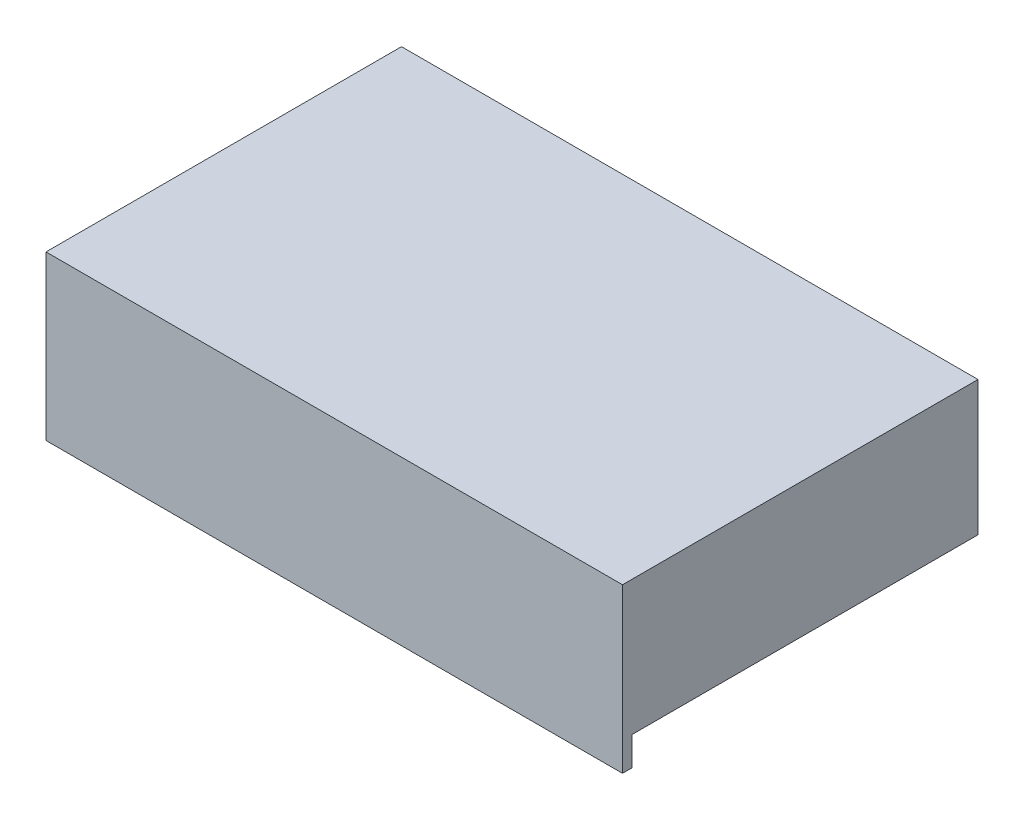
SolidWorks part; units mm, degrees
ref_plane "Front Plane" through (0, 0, 0) normal (0, 0, 1) x (1, 0, 0)
ref_plane "Top Plane" through (0, 0, 0) normal (0, 1, 0) x (1, 0, 0)
ref_plane "Right Plane" through (0, 0, 0) normal (1, 0, 0) x (0, 0, -1)
sketch "Sketch1" plane through (0, 0, 0) normal (0, 1, 0) x (1, 0, 0)
  line L1 (381, -228.6) -> (-381, -228.6)
  line L2 (381, -228.6) -> (381, 228.6)
  line L3 (381, 228.6) -> (-381, 228.6)
  line L4 (-381, -228.6) -> (-381, 228.6)
  line L5 (381, -228.6) -> (-381, 228.6) construction
  line L6 (381, 228.6) -> (-381, -228.6) construction
  point P0 (0, 0)
  dimension "D1" = 762
  dimension "D2" = 457.2
extrude "Boss-Extrude1" add sketch "Sketch1" along normal blind 177.8
sketch "Sketch2" plane through (0, 0, 0) normal (0, -1, 0) x (1, 0, 0)
  line L0 (-381, -228.6) -> (-381, 228.6) construction
  line L1 (374.65, -222.25) -> (-374.65, -222.25)
  line L2 (374.65, -222.25) -> (374.65, 222.25)
  line L3 (374.65, 222.25) -> (-374.65, 222.25)
  line L4 (-374.65, -222.25) -> (-374.65, 222.25)
  line L5 (374.65, -222.25) -> (-374.65, 222.25) construction
  line L6 (374.65, 222.25) -> (-374.65, -222.25) construction
  line L7 (-381, 228.6) -> (381, 228.6) construction
  point P0 (0, 0)
  dimension "D1" = 6.35
  dimension "D2" = 6.35
extrude "Cut-Extrude1" cut sketch "Sketch2" against normal blind 171.45
sketch "Sketch4" plane through (0, 0, 0) normal (0, -1, 0) x (1, 0, 0)
  line L0 (-381, 228.6) -> (381, 228.6) construction
  line L1 (379.4125, -227.0125) -> (-379.4125, -227.0125)
  line L2 (379.4125, -227.0125) -> (379.4125, 227.0125)
  line L3 (379.4125, 227.0125) -> (-379.4125, 227.0125)
  line L4 (-379.4125, -227.0125) -> (-379.4125, 227.0125)
  line L7 (-381, -228.6) -> (-381, 228.6) construction
  line L8 (-374.65, 222.25) -> (-374.65, -222.25) construction
  line L9 (376.2375, -223.8375) -> (-376.2375, -223.8375)
  line L10 (376.2375, -223.8375) -> (376.2375, 223.8375)
  line L11 (376.2375, 223.8375) -> (-376.2375, 223.8375)
  line L12 (-376.2375, -223.8375) -> (-376.2375, 223.8375)
  line L15 (374.65, 222.25) -> (-374.65, 222.25) construction
  point P0 (0, 0)
  point P10 (0, 0)
  dimension "D1" = 1.5875
  dimension "D2" = 1.5875
  dimension "D3" = 1.5875
  dimension "D4" = 1.5875
extrude "Cut-Extrude3" cut sketch "Sketch4" against normal blind 3.175
sketch "Sketch5" plane through (0, 0, 0) normal (0, 1, 0) x (1, 0, 0)
  line L0 (-1000, 0) -> (49000, 0) construction
  line L1 (0, -1000) -> (0, 49000) construction
  line L2 (-381, -228.6) -> (381, -228.6) construction
  line L4 (-381, -228.6) -> (381, -228.6)
  line L5 (-381, -228.6) -> (-381, -241.3)
  line L6 (-381, -241.3) -> (381, -241.3)
  line L7 (381, -228.6) -> (381, -241.3)
  dimension "D1" = 12.7
extrude "Boss-Extrude2" add sketch "Sketch5" along normal blind 177.8 and the other way blind 38.1
sketch "Sketch7" plane through (-381, 0, 0) normal (-1, 0, 0) x (0, 0, 1)
  line L0 (-228.6, 0) -> (228.6, 0) construction
  line L1 (-228.6, 177.8) -> (-228.6, 0) construction
  line L2 (-238.125, 9.525) -> (-238.125, 47.625)
  line L3 (-238.125, 47.625) -> (-228.6, 47.625)
  line L4 (-228.6, 47.625) -> (-228.6, 0)
  arc A0 (-238.125, 9.525) -> (-228.6, 0) centre (-238.125, 0) ccw
  circle A1 centre (-238.125, 0) radius 6.35
  arc A2 (-228.6, 0) -> (-238.125, 9.525) centre (-238.125, 0) ccw construction
  dimension "D1" = 19.05
  dimension "D2" = 12.7
  dimension "D3" = 38.1
extrude "Boss-Extrude3" add sketch "Sketch7" against normal blind 762
sketch "Sketch8" plane through (0, 177.8, 0) normal (0, 1, 0) x (1, 0, 0)
  line L0 (0, -1000) -> (0, 228.6) construction
  line L1 (-1000, 228.6) -> (49000, 228.6) construction
  line L4 (-120.65, 266.7) -> (-133.35, 266.7)
  line L5 (-133.35, 266.7) -> (-133.35, 228.6)
  line L6 (-190.5, 266.7) -> (-190.5, 228.6) construction
  line L12 (-146.05, 228.6) -> (-146.05, 266.7)
  line L13 (-146.05, 266.7) -> (-158.75, 266.7)
  line L14 (-158.75, 266.7) -> (-158.75, 228.6)
  line L15 (-247.65, 228.6) -> (-260.35, 228.6)
  line L16 (-171.45, 228.6) -> (-171.45, 266.7)
  line L17 (-171.45, 266.7) -> (-184.15, 266.7)
  line L18 (-184.15, 266.7) -> (-184.15, 228.6)
  line L19 (-184.15, 228.6) -> (-171.45, 228.6)
  line L20 (-158.75, 228.6) -> (-146.05, 228.6)
  line L21 (-133.35, 228.6) -> (-120.65, 228.6)
  line L22 (-247.65, 266.7) -> (-247.65, 228.6)
  line L23 (-260.35, 266.7) -> (-247.65, 266.7)
  line L24 (-222.25, 266.7) -> (-222.25, 228.6)
  line L25 (-234.95, 266.7) -> (-222.25, 266.7)
  line L26 (-234.95, 228.6) -> (-234.95, 266.7)
  line L27 (-222.25, 228.6) -> (-234.95, 228.6)
  line L28 (-196.85, 228.6) -> (-209.55, 228.6)
  line L29 (-196.85, 266.7) -> (-196.85, 228.6)
  line L30 (-209.55, 266.7) -> (-196.85, 266.7)
  line L31 (-209.55, 228.6) -> (-209.55, 266.7)
  line L32 (-381, 228.6) -> (-381, 247.65) construction
  line L33 (-381, 247.65) -> (-381, 228.6) construction
  line L34 (133.35, 266.7) -> (133.35, 228.6)
  line L35 (-260.35, 228.6) -> (-381, 228.6)
  line L37 (-260.35, 266.7) -> (-381, 266.7)
  line L38 (-381, 228.6) -> (-381, 266.7)
  line L39 (-120.65, 228.6) -> (120.65, 228.6)
  line L41 (-120.65, 266.7) -> (120.65, 266.7)
  line L43 (120.65, 266.7) -> (133.35, 266.7)
  line L44 (133.35, 228.6) -> (120.65, 228.6)
  line L45 (158.75, 228.6) -> (146.05, 228.6)
  line L46 (146.05, 266.7) -> (158.75, 266.7)
  line L47 (146.05, 228.6) -> (146.05, 266.7)
  line L48 (158.75, 266.7) -> (158.75, 228.6)
  line L49 (184.15, 228.6) -> (171.45, 228.6)
  line L50 (184.15, 266.7) -> (184.15, 228.6)
  line L51 (171.45, 266.7) -> (184.15, 266.7)
  line L52 (171.45, 228.6) -> (171.45, 266.7)
  line L53 (196.85, 266.7) -> (196.85, 228.6)
  line L54 (209.55, 266.7) -> (196.85, 266.7)
  line L55 (209.55, 228.6) -> (209.55, 266.7)
  line L56 (196.85, 228.6) -> (209.55, 228.6)
  line L57 (234.95, 266.7) -> (222.25, 266.7)
  line L58 (234.95, 228.6) -> (234.95, 266.7)
  line L59 (222.25, 228.6) -> (234.95, 228.6)
  line L60 (222.25, 266.7) -> (222.25, 228.6)
  line L61 (247.65, 266.7) -> (247.65, 228.6)
  line L62 (260.35, 266.7) -> (247.65, 266.7)
  line L63 (260.35, 266.7) -> (381, 266.7)
  line L64 (381, 228.6) -> (381, 266.7)
  line L65 (260.35, 228.6) -> (381, 228.6)
  line L66 (247.65, 228.6) -> (260.35, 228.6)
  line L67 (0, 266.7) -> (0, 49000) construction
  dimension "D1" = 38.1
  dimension "D3" = 12.7
  dimension "D4" = 12.7
  dimension "D5" = 12.7
  dimension "D6" = 12.7
  dimension "D7" = 12.7
extrude "Cut-Extrude4" cut sketch "Sketch8" against normal blind 202.692
sketch "Sketch9" plane through (0, 171.45, 0) normal (0, -1, 0) x (1, 0, 0)
  line L0 (-1000, 0) -> (49000, 0) construction
  line L5 (0, -1000) -> (0, 0) construction
  line L6 (0, 114.3) -> (0, 49000) construction
  circle A0 centre (-114.3, 68.58) radius 12.7
  circle A1 centre (-114.3, 68.58) radius 19.05
  circle A2 centre (114.3, 68.58) radius 12.7
  circle A3 centre (114.3, 68.58) radius 19.05
  circle A4 centre (-114.3, -68.58) radius 12.7
  circle A5 centre (-114.3, -68.58) radius 19.05
  circle A6 centre (114.3, -68.58) radius 19.05
  circle A7 centre (114.3, -68.58) radius 12.7
  point P0 (0, 0)
  dimension "D3" = 25.4
  dimension "D4" = 38.1
  dimension "D5" = 114.3
  dimension "D6" = 68.58
